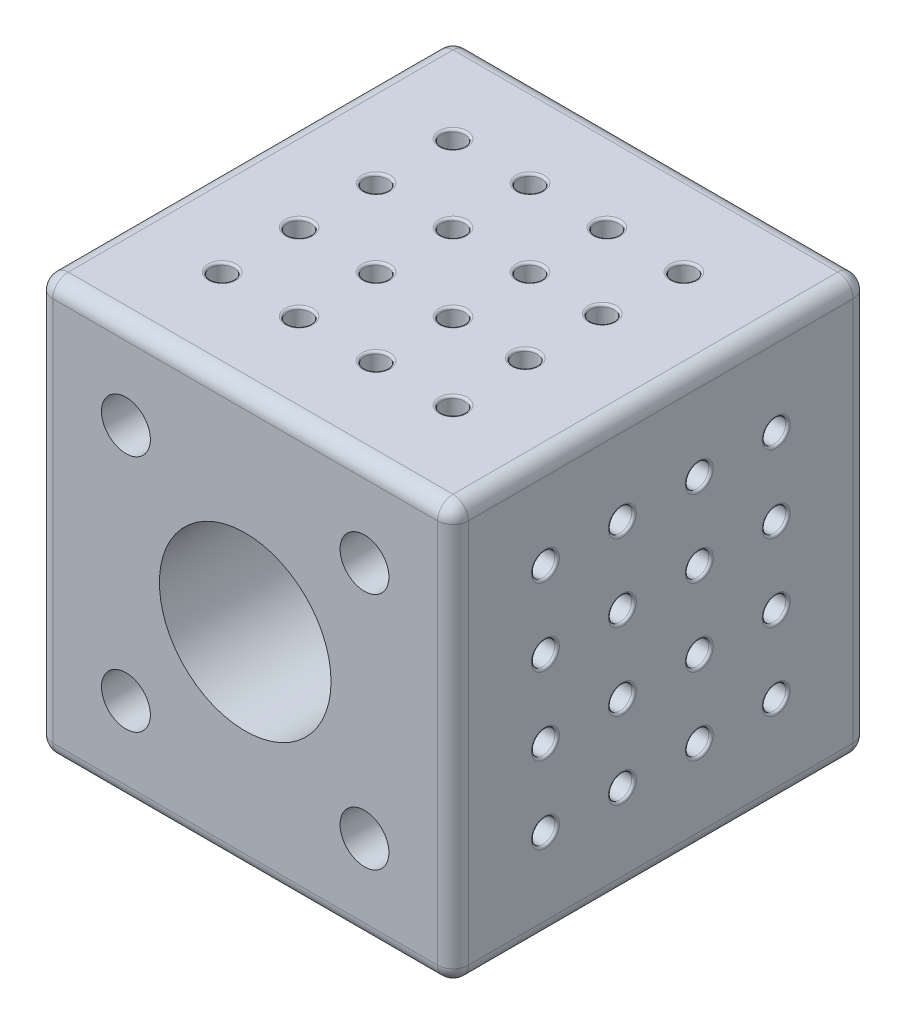
SolidWorks part; units mm, degrees
ref_plane "Front Plane" through (0, 0, 0) normal (0, 0, 1) x (1, 0, 0)
ref_plane "Top Plane" through (0, 0, 0) normal (0, 1, 0) x (1, 0, 0)
ref_plane "Right Plane" through (0, 0, 0) normal (1, 0, 0) x (0, 0, -1)
sketch "Sketch2" plane through (0, 0, 0) normal (0, 0, 1) x (1, 0, 0)
  line L1 (-21.7752, 34.5176) -> (32.2248, 34.5176)
  line L2 (-21.7752, 34.5176) -> (-21.7752, -19.4824)
  line L3 (-21.7752, -19.4824) -> (32.2248, -19.4824)
  line L4 (32.2248, 34.5176) -> (32.2248, -19.4824)
  dimension "D1" = 54
  dimension "D2" = 54
extrude "Boss-Extrude1" add sketch "Sketch2" along normal blind 54 and the other way blind 0.0001
fillet "Fillet1" radius 2 4 edges at (-21.7752, -19.4824, 26.9999) (-21.7752, 34.5176, 26.9999) (32.2248, -19.4824, 26.9999) (32.2248, 34.5176, 26.9999)
fillet "Fillet2" radius 2 16 edges at (31.6391, -18.8966, -0.0001) (-21.1894, -18.8966, -0.0001) (-21.1894, 33.9319, -0.0001) (31.6391, 33.9319, -0.0001) (-21.1894, -18.8966, 54) (-21.1894, 33.9319, 54) (31.6391, 33.9319, 54) (31.6391, -18.8966, 54) (5.2248, 34.5176, -0.0001) (-21.7752, 7.5176, -0.0001) (5.2248, -19.4824, -0.0001) (32.2248, 7.5176, -0.0001) (5.2248, 34.5176, 54) (32.2248, 7.5176, 54) (-21.7752, 7.5176, 54) (5.2248, -19.4824, 54)
sketch "Sketch4" plane through (0, 0, -0.0001) normal (0, 0, -1) x (-1, 0, 0)
  line L0 (19.7752, -17.4824) -> (19.7752, 32.5176) construction
  line L1 (19.7752, 32.5176) -> (-30.2248, 32.5176) construction
  circle A0 centre (-5.2248, 7.5176) radius 11.15
  circle A1 centre (-5.2248, 7.5176) radius 6.075
  dimension "D1" = 22.3
  dimension "D2" = 25
  dimension "D3" = 25
  dimension "D4" = 12.15
extrude "Cut-Extrude1" cut sketch "Sketch4" against normal blind 17 contours A0
sketch "Sketch12" plane through (0, 0, -0.0001) normal (0, 0, -1) x (-1, 0, 0)
  line L0 (-30.2248, 32.5176) -> (-30.2248, -17.4824) construction
  line L1 (-30.2248, -17.4824) -> (19.7752, -17.4824) construction
  line L2 (19.7752, -17.4824) -> (19.7752, 32.5176) construction
  circle A0 centre (-20.7248, 23.0176) radius 6.2
  circle A1 centre (10.2752, 23.0176) radius 6.2
  circle A2 centre (-20.7248, -7.9824) radius 6.2
  circle A3 centre (10.2752, -7.9824) radius 6.2
  dimension "D1" = 12.4
  dimension "D2" = 12.4
  dimension "D4" = 9.5
  dimension "D5" = 12.4
  dimension "D6" = 9.5
  dimension "D7" = 12.4
  dimension "D3" = 31
  dimension "D8" = 31
  dimension "D9" = 31
  dimension "D10" = 31
  dimension "D12" = 9.5
extrude "Cut-Extrude2" cut sketch "Sketch12" against normal blind 33.5
sketch "Sketch13" plane through (0, 0, 33.4999) normal (0, 0, -1) x (-1, 0, 0)
  circle A0 centre (-20.7248, 23.0176) radius 3.175
  circle A1 centre (10.2752, 23.0176) radius 3.175
  circle A2 centre (10.2752, -7.9824) radius 3.175
  circle A3 centre (-20.7248, -7.9824) radius 3.175
  dimension "D1" = 6.35
  dimension "D2" = 6.35
  dimension "D3" = 6.35
  dimension "D4" = 6.35
extrude "Cut-Extrude3" cut sketch "Sketch13" against normal through all
sketch "Sketch14" plane through (0, 0, 16.9999) normal (0, 0, -1) x (-1, 0, 0)
  line L0 (-5.2248, 7.5176) -> (-5.2248, 18.6676) construction
  line L1 (-5.2248, 18.6676) -> (-5.2248, -3.6324) construction
  line L2 (-5.2248, -3.6324) -> (-5.2248, 7.5176) construction
  line L3 (-5.2248, 7.5176) -> (-16.3748, 7.5176) construction
  line L4 (-16.3748, 7.5176) -> (5.9252, 7.5176) construction
  circle A0 centre (-5.2248, 7.5176) radius 11.15 construction
  circle A1 centre (-5.2248, 7.5176) radius 11.15 construction
sketch "Sketch15" plane through (0, 0, 16.9999) normal (0, 0, -1) x (-1, 0, 0)
  line L0 (-5.2248, 7.5176) -> (-5.2248, 18.6676) construction
  line L1 (-5.2248, 7.5176) -> (-16.3748, 7.5176) construction
  line L2 (-5.2248, 18.6676) -> (-5.2248, -3.6324) construction
  line L3 (-16.3748, 7.5176) -> (5.9252, 7.5176) construction
  circle A0 centre (-5.2248, 15.3676) radius 1.5
  circle A1 centre (-13.3748, 7.5176) radius 1.5
  circle A2 centre (-5.2248, -0.6324) radius 1.5
  circle A3 centre (2.6252, 7.5176) radius 1.5
  dimension "D1" = 3
  dimension "D2" = 3
  dimension "D3" = 3
  dimension "D4" = 3
  dimension "D5" = 16
  dimension "D6" = 16
  dimension "D7" = 3
  dimension "D8" = 3
extrude "Cut-Extrude4" cut sketch "Sketch15" against normal through all
sketch "Sketch16" plane through (0, 0, 16.9999) normal (0, 0, -1) x (-1, 0, 0)
  circle A0 centre (-5.2248, 7.5176) radius 6.075
  dimension "D1" = 12.15
extrude "Cut-Extrude5" cut sketch "Sketch16" against normal through all
sketch "Sketch17" plane through (0, 0, 54) normal (0, 0, 1) x (1, 0, 0)
  circle A0 centre (5.2248, 7.5176) radius 11.15
  dimension "D1" = 22.3
extrude "Cut-Extrude6" cut sketch "Sketch17" against normal blind 18
sketch "Sketch18" plane through (0, 0, 16.9999) normal (0, 0, -1) x (-1, 0, 0)
  circle A1 centre (-5.2248, 7.5176) radius 11.1
extrude "Cut-Extrude7" cut sketch "Sketch18" against normal blind 1
sketch "Sketch19" plane through (0, 34.5176, 0) normal (0, 1, 0) x (1, 0, 0)
  line L0 (30.2248, -1.9999) -> (-19.7752, -1.9999) construction
  line L1 (-19.7752, -1.9999) -> (-19.7752, -52) construction
  line L3 (30.2248, -52) -> (30.2248, -1.9999) construction
  line L4 (-19.7752, -52) -> (30.2248, -52) construction
  circle A0 centre (-9.7752, -11.9999) radius 1.525
  circle A1 centre (0.2248, -11.9999) radius 1.525
  circle A2 centre (10.2248, -11.9999) radius 1.525
  circle A3 centre (20.2248, -11.9999) radius 1.525
  circle A4 centre (-9.7752, -21.9999) radius 1.525
  circle A5 centre (0.2248, -21.9999) radius 1.525
  circle A6 centre (10.2248, -21.9999) radius 1.525
  circle A7 centre (19.61, -21.9999) radius 1.525
  circle A8 centre (-9.7752, -31.9999) radius 1.525
  circle A9 centre (0.2248, -31.9999) radius 1.525
  circle A10 centre (10.2248, -31.9999) radius 1.525
  circle A11 centre (19.61, -31.9999) radius 1.525
  circle A12 centre (-9.7752, -41.9999) radius 1.525
  circle A13 centre (0.2248, -41.9999) radius 1.525
  circle A14 centre (10.2248, -42) radius 1.525
  circle A15 centre (20.2248, -42) radius 1.525
  dimension "D1" = 3.05
  dimension "D2" = 10
  dimension "D3" = 10
  dimension "D4" = 3.05
  dimension "D6" = 3.05
  dimension "D8" = 3.05
  dimension "D12" = 3.05
  dimension "D14" = 3.05
  dimension "D17" = 3.05
  dimension "D18" = 3.05
  dimension "D20" = 3.05
  dimension "D21" = 3.05
  dimension "D22" = 3.05
  dimension "D23" = 3.05
  dimension "D24" = 3.05
  dimension "D28" = 3.05
  dimension "D29" = 3.05
  dimension "D30" = 3.05
  dimension "D5" = 10
  dimension "D7" = 10
  dimension "D9" = 10
  dimension "D10" = 10
  dimension "D11" = 10
  dimension "D13" = 10
  dimension "D15" = 10
  dimension "D16" = 10
  dimension "D19" = 10
  dimension "D25" = 10
  dimension "D26" = 10
  dimension "D27" = 10.0001
  dimension "D31" = 10
  dimension "D32" = 10
  dimension "D33" = 10
extrude "Cut-Extrude8" cut sketch "Sketch19" against normal blind 4
sketch "Sketch21" plane through (32.2248, 0, 0) normal (1, 0, 0) x (0, -1, 0)
  line L2 (-32.5176, -52) -> (17.4824, -52) construction
  line L5 (-32.5176, -1.9999) -> (-32.5176, -52) construction
  line L6 (17.4824, -1.9999) -> (-32.5176, -1.9999) construction
  line L7 (17.4824, -52) -> (17.4824, -1.9999) construction
  circle A0 centre (-22.5176, -12) radius 1.525
  circle A1 centre (-12.5176, -12) radius 1.525
  circle A2 centre (-2.5176, -12) radius 1.525
  circle A3 centre (7.4824, -12) radius 1.525
  circle A4 centre (-22.5176, -22) radius 1.525
  circle A5 centre (-12.5176, -22) radius 1.525
  circle A6 centre (-2.5176, -22) radius 1.525
  circle A7 centre (7.4824, -22) radius 1.525
  circle A8 centre (-22.5176, -32) radius 1.525
  circle A9 centre (-12.5176, -32) radius 1.525
  circle A10 centre (-2.5176, -32) radius 1.525
  circle A11 centre (7.4824, -32) radius 1.525
  circle A12 centre (-22.5176, -42) radius 1.525
  circle A13 centre (-12.5176, -42) radius 1.525
  circle A14 centre (-2.5176, -42) radius 1.525
  circle A15 centre (7.4824, -42) radius 1.525
  dimension "D1" = 3.05
  dimension "D4" = 3.05
  dimension "D6" = 3.05
  dimension "D8" = 3.05
  dimension "D12" = 3.05
  dimension "D14" = 3.05
  dimension "D17" = 3.05
  dimension "D18" = 3.05
  dimension "D20" = 3.05
  dimension "D21" = 3.05
  dimension "D22" = 3.05
  dimension "D23" = 3.05
  dimension "D24" = 3.05
  dimension "D28" = 3.05
  dimension "D29" = 3.05
  dimension "D30" = 3.05
  dimension "D5" = 10
  dimension "D7" = 10
  dimension "D9" = 10
  dimension "D10" = 10
  dimension "D11" = 10
  dimension "D13" = 10
  dimension "D15" = 10
  dimension "D16" = 10
  dimension "D19" = 10
  dimension "D25" = 10
  dimension "D26" = 10
  dimension "D27" = 10.0001
  dimension "D31" = 10
  dimension "D32" = 10
  dimension "D33" = 10
  dimension "D34" = 10
  dimension "D35" = 10
  dimension "D36" = 10
  dimension "D37" = 10
  dimension "D38" = 10.0001
  dimension "D39" = 10
  dimension "D40" = 10
  dimension "D41" = 10
  dimension "D42" = 10
  dimension "D43" = 10
  dimension "D44" = 10
  dimension "D45" = 10
  dimension "D46" = 10.0001
  dimension "D47" = 10
  dimension "D48" = 10
  dimension "D49" = 10
  dimension "D50" = 10
  dimension "D51" = 10
  dimension "D52" = 10
  dimension "D53" = 10
  dimension "D54" = 10
  dimension "D55" = 10
  dimension "D56" = 10.0001
  dimension "D57" = 10
extrude "Cut-Extrude10" cut sketch "Sketch21" against normal blind 4
sketch "Sketch22" plane through (0, -19.4824, 0) normal (0, -1, 0) x (0, 0, 1)
  line L0 (1.9999, 19.7752) -> (1.9999, -30.2248) construction
  line L1 (52, 19.7752) -> (1.9999, 19.7752) construction
  line L2 (52, -30.2248) -> (52, 19.7752) construction
  line L3 (1.9999, -30.2248) -> (52, -30.2248) construction
  circle A0 centre (11.9999, 9.7752) radius 1.525
  circle A1 centre (21.9999, 9.7752) radius 1.525
  circle A2 centre (31.9999, 9.7752) radius 1.525
  circle A3 centre (41.9999, 9.7752) radius 1.525
  circle A4 centre (11.9999, -0.2248) radius 1.525
  circle A5 centre (21.9999, -0.2248) radius 1.525
  circle A6 centre (31.9999, -0.2248) radius 1.525
  circle A7 centre (41.9999, -0.2248) radius 1.525
  circle A8 centre (11.9999, -10.2248) radius 1.525
  circle A9 centre (21.9999, -10.2248) radius 1.525
  circle A10 centre (31.9999, -10.2248) radius 1.525
  circle A11 centre (41.9999, -10.2248) radius 1.525
  circle A12 centre (11.9999, -20.2248) radius 1.525
  circle A13 centre (21.9999, -20.2248) radius 1.525
  circle A14 centre (31.9999, -20.2248) radius 1.525
  circle A15 centre (41.9999, -20.2248) radius 1.525
  dimension "D1" = 3.05
  dimension "D4" = 3.05
  dimension "D6" = 3.05
  dimension "D8" = 3.05
  dimension "D12" = 3.05
  dimension "D14" = 3.05
  dimension "D17" = 3.05
  dimension "D18" = 3.05
  dimension "D20" = 3.05
  dimension "D21" = 3.05
  dimension "D22" = 3.05
  dimension "D23" = 3.05
  dimension "D24" = 3.05
  dimension "D28" = 3.05
  dimension "D29" = 3.05
  dimension "D30" = 3.05
  dimension "D5" = 10
  dimension "D7" = 10
  dimension "D9" = 10
  dimension "D10" = 10
  dimension "D11" = 10
  dimension "D13" = 10
  dimension "D15" = 10
  dimension "D16" = 10
  dimension "D19" = 10
  dimension "D25" = 10
  dimension "D26" = 10.0001
  dimension "D27" = 10
  dimension "D31" = 10
  dimension "D32" = 10
  dimension "D33" = 10.0001
  dimension "D34" = 10
  dimension "D35" = 10
  dimension "D36" = 10
  dimension "D37" = 10
  dimension "D38" = 10
  dimension "D40" = 10
  dimension "D41" = 10
  dimension "D42" = 10
  dimension "D43" = 10
  dimension "D44" = 10
  dimension "D45" = 10
  dimension "D47" = 10
  dimension "D50" = 10
  dimension "D51" = 10
  dimension "D52" = 10
  dimension "D53" = 10
  dimension "D54" = 10
  dimension "D55" = 10
extrude "Cut-Extrude11" cut sketch "Sketch22" against normal blind 4
sketch "Sketch25" plane through (-21.7752, 0, 0) normal (-1, 0, 0) x (0, 0, 1)
  line L4 (52, 32.5176) -> (1.9999, 32.5176) construction
  line L5 (1.9999, 32.5176) -> (1.9999, -17.4824) construction
  line L6 (1.9999, -17.4824) -> (52, -17.4824) construction
  line L7 (52, -17.4824) -> (52, 32.5176) construction
  circle A0 centre (11.9999, 22.5176) radius 1.525
  circle A1 centre (21.9999, 22.5176) radius 1.525
  circle A2 centre (31.9999, 22.5176) radius 1.525
  circle A3 centre (41.9999, 22.5176) radius 1.525
  circle A4 centre (11.9999, 12.5176) radius 1.525
  circle A5 centre (21.9999, 12.5176) radius 1.525
  circle A6 centre (31.9999, 12.5176) radius 1.525
  circle A7 centre (41.9999, 12.5176) radius 1.525
  circle A8 centre (11.9999, 2.5176) radius 1.525
  circle A9 centre (21.9999, 2.5176) radius 1.525
  circle A10 centre (31.9999, 2.5176) radius 1.525
  circle A11 centre (41.9999, 2.5176) radius 1.525
  circle A12 centre (11.9999, -7.4824) radius 1.525
  circle A13 centre (21.9999, -7.4824) radius 1.525
  circle A14 centre (31.9999, -7.4824) radius 1.525
  circle A15 centre (41.9999, -7.4824) radius 1.525
  dimension "D1" = 3.05
  dimension "D4" = 3.05
  dimension "D6" = 3.05
  dimension "D8" = 3.05
  dimension "D12" = 3.05
  dimension "D14" = 3.05
  dimension "D17" = 3.05
  dimension "D18" = 3.05
  dimension "D20" = 3.05
  dimension "D21" = 3.05
  dimension "D22" = 3.05
  dimension "D23" = 3.05
  dimension "D24" = 3.05
  dimension "D28" = 3.05
  dimension "D29" = 3.05
  dimension "D30" = 3.05
  dimension "D5" = 10
  dimension "D7" = 10
  dimension "D9" = 10
  dimension "D10" = 10
  dimension "D11" = 10
  dimension "D13" = 10
  dimension "D15" = 10
  dimension "D16" = 10
  dimension "D19" = 10
  dimension "D25" = 10
  dimension "D26" = 10
  dimension "D27" = 10
  dimension "D31" = 10
  dimension "D32" = 10
  dimension "D33" = 10.0001
  dimension "D34" = 10
  dimension "D35" = 10
  dimension "D36" = 10
  dimension "D37" = 10
  dimension "D38" = 10
  dimension "D40" = 10
  dimension "D41" = 10
  dimension "D42" = 10
  dimension "D43" = 10
  dimension "D44" = 10
  dimension "D45" = 10
  dimension "D47" = 10
  dimension "D50" = 10
  dimension "D51" = 10
  dimension "D52" = 10
  dimension "D53" = 10
  dimension "D54" = 10
  dimension "D55" = 10
extrude "Cut-Extrude13" cut sketch "Sketch25" against normal blind 4
fillet "Fillet3" radius 0.3 32 edges at (-21.7752, 20.9926, 11.9999) (-17.7752, 20.9926, 11.9999) (-21.7752, -9.0074, 11.9999) (-17.7752, -9.0074, 11.9999) (-21.7752, 0.9926, 41.9999) (-17.7752, 0.9926, 41.9999) (-21.7752, 0.9926, 31.9999) (-17.7752, 0.9926, 31.9999) (-21.7752, 0.9926, 21.9999) (-17.7752, 0.9926, 21.9999) (-21.7752, -9.0074, 21.9999) (-17.7752, -9.0074, 21.9999) (-21.7752, -9.0074, 31.9999) (-17.7752, -9.0074, 31.9999) (-21.7752, -9.0074, 41.9999) (-17.7752, -9.0074, 41.9999) (-21.7752, 10.9926, 21.9999) (-17.7752, 10.9926, 21.9999) (-21.7752, 20.9926, 41.9999) (-17.7752, 20.9926, 41.9999) (-21.7752, 20.9926, 31.9999) (-17.7752, 20.9926, 31.9999) (-21.7752, 20.9926, 21.9999) (-17.7752, 20.9926, 21.9999) (-21.7752, 0.9926, 11.9999) (-17.7752, 0.9926, 11.9999) (-21.7752, 10.9926, 41.9999) (-17.7752, 10.9926, 41.9999) (-21.7752, 10.9926, 31.9999) (-17.7752, 10.9926, 31.9999) (-21.7752, 10.9926, 11.9999) (-17.7752, 10.9926, 11.9999)
fillet "Fillet4" radius 0.3 32 edges at (-9.7752, -19.4824, 10.4749) (-9.7752, -15.4824, 10.4749) (20.2248, -19.4824, 10.4749) (20.2248, -15.4824, 10.4749) (10.2248, -19.4824, 40.4749) (10.2248, -15.4824, 40.4749) (10.2248, -19.4824, 30.4749) (10.2248, -15.4824, 30.4749) (10.2248, -19.4824, 20.4749) (10.2248, -15.4824, 20.4749) (20.2248, -19.4824, 20.4749) (20.2248, -15.4824, 20.4749) (20.2248, -19.4824, 30.4749) (20.2248, -15.4824, 30.4749) (20.2248, -19.4824, 40.4749) (20.2248, -15.4824, 40.4749) (0.2248, -19.4824, 20.4749) (0.2248, -15.4824, 20.4749) (-9.7752, -19.4824, 40.4749) (-9.7752, -15.4824, 40.4749) (-9.7752, -19.4824, 30.4749) (-9.7752, -15.4824, 30.4749) (-9.7752, -19.4824, 20.4749) (-9.7752, -15.4824, 20.4749) (10.2248, -19.4824, 10.4749) (10.2248, -15.4824, 10.4749) (0.2248, -19.4824, 40.4749) (0.2248, -15.4824, 40.4749) (0.2248, -19.4824, 30.4749) (0.2248, -15.4824, 30.4749) (0.2248, -19.4824, 10.4749) (0.2248, -15.4824, 10.4749)
fillet "Fillet5" radius 0.3 32 edges at (32.2248, 22.5176, 10.475) (28.2248, 22.5176, 10.475) (32.2248, 22.5176, 40.475) (28.2248, 22.5176, 40.475) (32.2248, -7.4824, 30.475) (28.2248, -7.4824, 30.475) (32.2248, 2.5176, 30.475) (28.2248, 2.5176, 30.475) (32.2248, 12.5176, 30.475) (28.2248, 12.5176, 30.475) (32.2248, 12.5176, 40.475) (28.2248, 12.5176, 40.475) (32.2248, 2.5176, 40.475) (28.2248, 2.5176, 40.475) (32.2248, -7.4824, 40.475) (28.2248, -7.4824, 40.475) (32.2248, 12.5176, 20.475) (28.2248, 12.5176, 20.475) (32.2248, -7.4824, 10.475) (28.2248, -7.4824, 10.475) (32.2248, 2.5176, 10.475) (28.2248, 2.5176, 10.475) (32.2248, 12.5176, 10.475) (28.2248, 12.5176, 10.475) (32.2248, 22.5176, 30.475) (28.2248, 22.5176, 30.475) (32.2248, -7.4824, 20.475) (28.2248, -7.4824, 20.475) (32.2248, 2.5176, 20.475) (28.2248, 2.5176, 20.475) (32.2248, 22.5176, 20.475) (28.2248, 22.5176, 20.475)
fillet "Fillet6" radius 0.3 32 edges at (-9.7752, 34.5176, 13.5249) (-9.7752, 30.5176, 13.5249) (-9.7752, 34.5176, 43.5249) (-9.7752, 30.5176, 43.5249) (19.61, 34.5176, 33.5249) (19.61, 30.5176, 33.5249) (10.2248, 34.5176, 33.5249) (10.2248, 30.5176, 33.5249) (0.2248, 34.5176, 33.5249) (0.2248, 30.5176, 33.5249) (0.2248, 34.5176, 43.5249) (0.2248, 30.5176, 43.5249) (10.2248, 34.5176, 43.525) (10.2248, 30.5176, 43.525) (20.2248, 34.5176, 43.525) (20.2248, 30.5176, 43.525) (0.2248, 34.5176, 23.5249) (0.2248, 30.5176, 23.5249) (20.2248, 34.5176, 13.5249) (20.2248, 30.5176, 13.5249) (10.2248, 34.5176, 13.5249) (10.2248, 30.5176, 13.5249) (0.2248, 34.5176, 13.5249) (0.2248, 30.5176, 13.5249) (-9.7752, 34.5176, 33.5249) (-9.7752, 30.5176, 33.5249) (19.61, 34.5176, 23.5249) (19.61, 30.5176, 23.5249) (10.2248, 34.5176, 23.5249) (10.2248, 30.5176, 23.5249) (-9.7752, 34.5176, 23.5249) (-9.7752, 30.5176, 23.5249)
